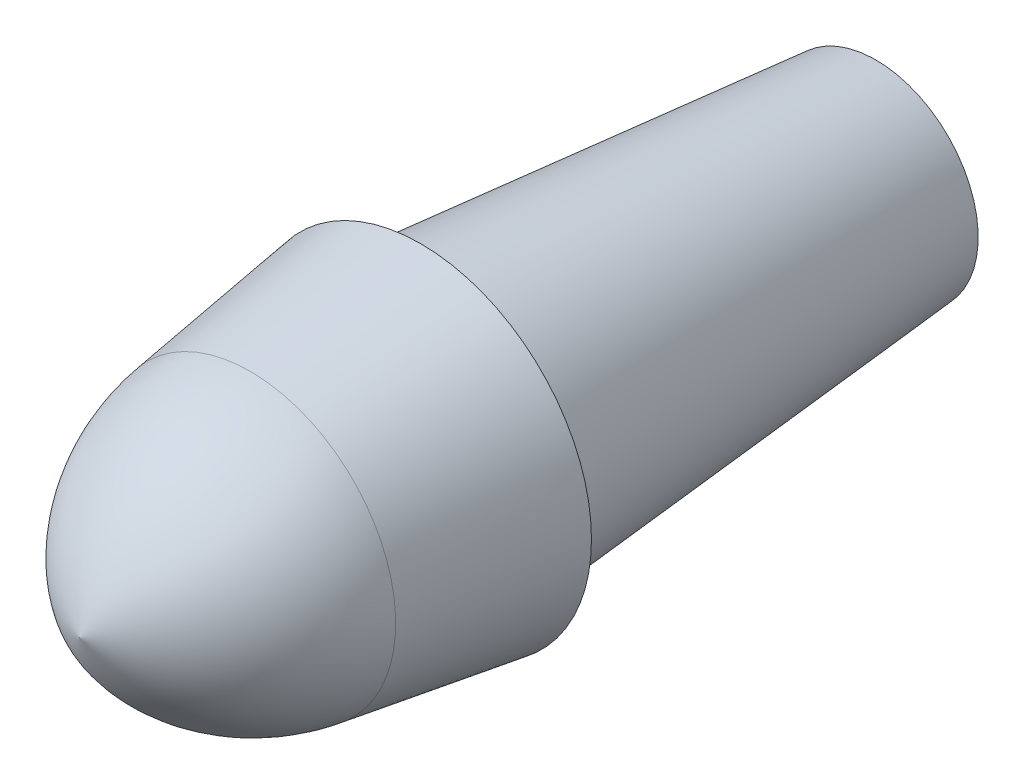
SolidWorks part; units mm, degrees
ref_plane "Front Plane" through (0, 0, 0) normal (0, 0, 1) x (1, 0, 0)
ref_plane "Top Plane" through (0, 0, 0) normal (0, 1, 0) x (1, 0, 0)
ref_plane "Right Plane" through (0, 0, 0) normal (1, 0, 0) x (0, 0, -1)
sketch "Sketch1" plane through (0, 0, 0) normal (0, 1, 0) x (1, 0, 0)
  line L0 (0, 0) -> (0, -30) construction
  line L1 (0, 0) -> (-7.5, 0)
  line L2 (-7.5, 0) -> (-6.3927, -7.5)
  line L3 (0, 0) -> (0, -15)
  arc A0 (-6.3927, -7.5) -> (0, -15) centre (2.7946, -6.1436) ccw
  point P7 (0, 0)
  dimension "D1" = 7.5
  dimension "D2" = 7.5
  dimension "D3" = 15
revolve "Revolve1" add sketch "Sketch1" angle 360 about L0
sketch "Sketch2" plane through (0, 0, 0) normal (0, 0, -1) x (-1, 0, 0)
  circle A0 centre (0, 0) radius 6.25
  dimension "D1" = 12.5
ref_plane "Plane2" through (0, 0, -20) normal (0, 0, -1) x (-1, 0, 0)
sketch "Sketch4" plane through (0, 0, -20) normal (0, 0, -1) x (-1, 0, 0)
  circle A0 centre (0, 0) radius 4.5
  dimension "D1" = 9
loft "Loft2" add profiles "Sketch2", "Sketch4"
